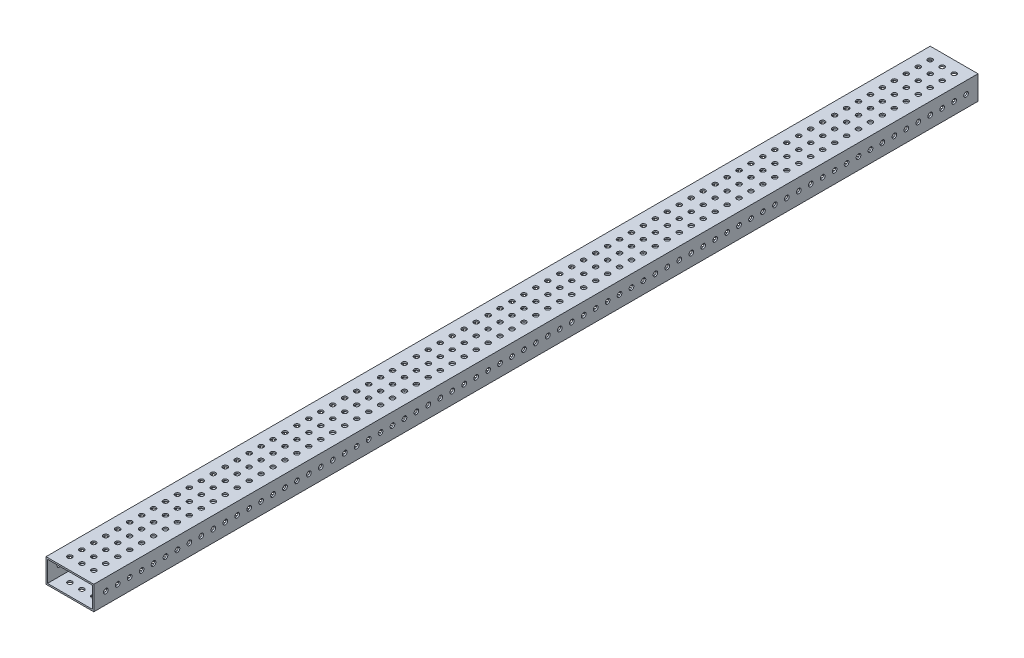
SolidWorks part; units mm, degrees
material "6061 Alloy"
ref_plane "Front Plane" through (0, 0, 0) normal (0, 0, 1) x (1, 0, 0)
ref_plane "Top Plane" through (0, 0, 0) normal (0, 1, 0) x (1, 0, 0)
ref_plane "Right Plane" through (0, 0, 0) normal (1, 0, 0) x (0, 0, -1)
sketch "Sketch1" plane through (0, 0, 0) normal (0, 0, 1) x (1, 0, 0)
  line L0 (1.5875, 1.5875) -> (49.2125, 1.5875)
  line L1 (0, 0) -> (50.8, 0)
  line L2 (0, 0) -> (0, 25.4)
  line L3 (0, 25.4) -> (50.8, 25.4)
  line L4 (50.8, 0) -> (50.8, 25.4)
  line L5 (49.2125, 1.5875) -> (49.2125, 23.8125)
  line L6 (1.5875, 23.8125) -> (49.2125, 23.8125)
  line L7 (1.5875, 1.5875) -> (1.5875, 23.8125)
  dimension "D1" = 50.8
  dimension "D2" = 25.4
  dimension "D3" = 1.5875
extrude "Boss-Extrude1" add sketch "Sketch1" along normal blind 939.8
sketch "Sketch2" plane through (50.8, 0, 0) normal (1, 0, 0) x (0, 0, -1)
  line L0 (-939.8, 0) -> (-939.8, 25.4) construction
  line L1 (-927.1, 12.7) -> (-914.4, 12.7) construction
  circle A0 centre (-927.1, 12.7) radius 2.4892
  circle A1 centre (-914.4, 12.7) radius 2.4892
  circle A2 centre (-901.7, 12.7) radius 2.4892
  circle A3 centre (-889, 12.7) radius 2.4892
  circle A4 centre (-876.3, 12.7) radius 2.4892
  circle A5 centre (-863.6, 12.7) radius 2.4892
  circle A6 centre (-850.9, 12.7) radius 2.4892
  circle A7 centre (-838.2, 12.7) radius 2.4892
  circle A8 centre (-825.5, 12.7) radius 2.4892
  circle A9 centre (-812.8, 12.7) radius 2.4892
  circle A10 centre (-800.1, 12.7) radius 2.4892
  circle A11 centre (-787.4, 12.7) radius 2.4892
  circle A12 centre (-774.7, 12.7) radius 2.4892
  circle A13 centre (-762, 12.7) radius 2.4892
  circle A14 centre (-749.3, 12.7) radius 2.4892
  circle A15 centre (-736.6, 12.7) radius 2.4892
  circle A16 centre (-723.9, 12.7) radius 2.4892
  circle A17 centre (-711.2, 12.7) radius 2.4892
  circle A18 centre (-698.5, 12.7) radius 2.4892
  circle A19 centre (-685.8, 12.7) radius 2.4892
  circle A20 centre (-673.1, 12.7) radius 2.4892
  circle A21 centre (-660.4, 12.7) radius 2.4892
  circle A22 centre (-647.7, 12.7) radius 2.4892
  circle A23 centre (-635, 12.7) radius 2.4892
  circle A24 centre (-622.3, 12.7) radius 2.4892
  circle A25 centre (-609.6, 12.7) radius 2.4892
  circle A26 centre (-596.9, 12.7) radius 2.4892
  circle A27 centre (-584.2, 12.7) radius 2.4892
  circle A28 centre (-571.5, 12.7) radius 2.4892
  circle A29 centre (-558.8, 12.7) radius 2.4892
  circle A30 centre (-546.1, 12.7) radius 2.4892
  circle A31 centre (-533.4, 12.7) radius 2.4892
  circle A32 centre (-520.7, 12.7) radius 2.4892
  circle A33 centre (-508, 12.7) radius 2.4892
  circle A34 centre (-495.3, 12.7) radius 2.4892
  circle A35 centre (-482.6, 12.7) radius 2.4892
  circle A36 centre (-469.9, 12.7) radius 2.4892
  circle A37 centre (-457.2, 12.7) radius 2.4892
  circle A38 centre (-444.5, 12.7) radius 2.4892
  circle A39 centre (-431.8, 12.7) radius 2.4892
  circle A40 centre (-419.1, 12.7) radius 2.4892
  circle A41 centre (-406.4, 12.7) radius 2.4892
  circle A42 centre (-393.7, 12.7) radius 2.4892
  circle A43 centre (-381, 12.7) radius 2.4892
  circle A44 centre (-368.3, 12.7) radius 2.4892
  circle A45 centre (-355.6, 12.7) radius 2.4892
  circle A46 centre (-342.9, 12.7) radius 2.4892
  circle A47 centre (-330.2, 12.7) radius 2.4892
  circle A48 centre (-317.5, 12.7) radius 2.4892
  circle A49 centre (-304.8, 12.7) radius 2.4892
  circle A50 centre (-292.1, 12.7) radius 2.4892
  circle A51 centre (-279.4, 12.7) radius 2.4892
  circle A52 centre (-266.7, 12.7) radius 2.4892
  circle A53 centre (-254, 12.7) radius 2.4892
  circle A54 centre (-241.3, 12.7) radius 2.4892
  circle A55 centre (-228.6, 12.7) radius 2.4892
  circle A56 centre (-215.9, 12.7) radius 2.4892
  circle A57 centre (-203.2, 12.7) radius 2.4892
  circle A58 centre (-190.5, 12.7) radius 2.4892
  circle A59 centre (-177.8, 12.7) radius 2.4892
  circle A60 centre (-165.1, 12.7) radius 2.4892
  circle A61 centre (-152.4, 12.7) radius 2.4892
  circle A62 centre (-139.7, 12.7) radius 2.4892
  circle A63 centre (-127, 12.7) radius 2.4892
  circle A64 centre (-114.3, 12.7) radius 2.4892
  circle A65 centre (-101.6, 12.7) radius 2.4892
  circle A66 centre (-88.9, 12.7) radius 2.4892
  circle A67 centre (-76.2, 12.7) radius 2.4892
  circle A68 centre (-63.5, 12.7) radius 2.4892
  circle A69 centre (-50.8, 12.7) radius 2.4892
  circle A70 centre (-38.1, 12.7) radius 2.4892
  circle A71 centre (-25.4, 12.7) radius 2.4892
  circle A72 centre (-12.7, 12.7) radius 2.4892
  point P4 (-939.8, 12.7)
  dimension "D1" = 4.9784
  dimension "D2" = 12.7
  dimension "D4" = 12.7
  dimension "D3" = 73
extrude "Cut-Extrude1" cut sketch "Sketch2" against normal through all
sketch "Sketch3" plane through (0, 25.4, 0) normal (0, 1, 0) x (1, 0, 0)
  line L0 (0, -939.8) -> (0, 0) construction
  line L1 (50.8, 0) -> (0, 0) construction
  line L2 (12.7, -12.7) -> (25.4, -12.7) construction
  line L3 (12.7, -12.7) -> (12.7, -25.4) construction
  circle A0 centre (12.7, -12.7) radius 2.4892
  circle A1 centre (25.4, -12.7) radius 2.4892
  circle A2 centre (38.1, -12.7) radius 2.4892
  circle A3 centre (25.4, -25.4) radius 2.4892
  circle A4 centre (38.1, -25.4) radius 2.4892
  circle A5 centre (25.4, -38.1) radius 2.4892
  circle A6 centre (38.1, -38.1) radius 2.4892
  circle A7 centre (25.4, -50.8) radius 2.4892
  circle A8 centre (38.1, -50.8) radius 2.4892
  circle A9 centre (25.4, -63.5) radius 2.4892
  circle A10 centre (38.1, -63.5) radius 2.4892
  circle A11 centre (25.4, -76.2) radius 2.4892
  circle A12 centre (38.1, -76.2) radius 2.4892
  circle A13 centre (25.4, -88.9) radius 2.4892
  circle A14 centre (38.1, -88.9) radius 2.4892
  circle A15 centre (25.4, -101.6) radius 2.4892
  circle A16 centre (38.1, -101.6) radius 2.4892
  circle A17 centre (25.4, -114.3) radius 2.4892
  circle A18 centre (38.1, -114.3) radius 2.4892
  circle A19 centre (25.4, -127) radius 2.4892
  circle A20 centre (38.1, -127) radius 2.4892
  circle A21 centre (25.4, -139.7) radius 2.4892
  circle A22 centre (38.1, -139.7) radius 2.4892
  circle A23 centre (25.4, -152.4) radius 2.4892
  circle A24 centre (38.1, -152.4) radius 2.4892
  circle A25 centre (25.4, -165.1) radius 2.4892
  circle A26 centre (38.1, -165.1) radius 2.4892
  circle A27 centre (25.4, -177.8) radius 2.4892
  circle A28 centre (38.1, -177.8) radius 2.4892
  circle A29 centre (25.4, -190.5) radius 2.4892
  circle A30 centre (38.1, -190.5) radius 2.4892
  circle A31 centre (25.4, -203.2) radius 2.4892
  circle A32 centre (38.1, -203.2) radius 2.4892
  circle A33 centre (25.4, -215.9) radius 2.4892
  circle A34 centre (38.1, -215.9) radius 2.4892
  circle A35 centre (25.4, -228.6) radius 2.4892
  circle A36 centre (38.1, -228.6) radius 2.4892
  circle A37 centre (25.4, -241.3) radius 2.4892
  circle A38 centre (38.1, -241.3) radius 2.4892
  circle A39 centre (25.4, -254) radius 2.4892
  circle A40 centre (38.1, -254) radius 2.4892
  circle A41 centre (25.4, -266.7) radius 2.4892
  circle A42 centre (38.1, -266.7) radius 2.4892
  circle A43 centre (25.4, -279.4) radius 2.4892
  circle A44 centre (38.1, -279.4) radius 2.4892
  circle A45 centre (25.4, -292.1) radius 2.4892
  circle A46 centre (38.1, -292.1) radius 2.4892
  circle A47 centre (25.4, -304.8) radius 2.4892
  circle A48 centre (38.1, -304.8) radius 2.4892
  circle A49 centre (25.4, -317.5) radius 2.4892
  circle A50 centre (38.1, -317.5) radius 2.4892
  circle A51 centre (25.4, -330.2) radius 2.4892
  circle A52 centre (38.1, -330.2) radius 2.4892
  circle A53 centre (25.4, -342.9) radius 2.4892
  circle A54 centre (38.1, -342.9) radius 2.4892
  circle A55 centre (25.4, -355.6) radius 2.4892
  circle A56 centre (38.1, -355.6) radius 2.4892
  circle A57 centre (25.4, -368.3) radius 2.4892
  circle A58 centre (38.1, -368.3) radius 2.4892
  circle A59 centre (25.4, -381) radius 2.4892
  circle A60 centre (38.1, -381) radius 2.4892
  circle A61 centre (25.4, -393.7) radius 2.4892
  circle A62 centre (38.1, -393.7) radius 2.4892
  circle A63 centre (25.4, -406.4) radius 2.4892
  circle A64 centre (38.1, -406.4) radius 2.4892
  circle A65 centre (25.4, -419.1) radius 2.4892
  circle A66 centre (38.1, -419.1) radius 2.4892
  circle A67 centre (25.4, -431.8) radius 2.4892
  circle A68 centre (38.1, -431.8) radius 2.4892
  circle A69 centre (25.4, -444.5) radius 2.4892
  circle A70 centre (38.1, -444.5) radius 2.4892
  circle A71 centre (25.4, -457.2) radius 2.4892
  circle A72 centre (38.1, -457.2) radius 2.4892
  circle A73 centre (25.4, -469.9) radius 2.4892
  circle A74 centre (38.1, -469.9) radius 2.4892
  circle A75 centre (25.4, -482.6) radius 2.4892
  circle A76 centre (38.1, -482.6) radius 2.4892
  circle A77 centre (25.4, -495.3) radius 2.4892
  circle A78 centre (38.1, -495.3) radius 2.4892
  circle A79 centre (25.4, -508) radius 2.4892
  circle A80 centre (38.1, -508) radius 2.4892
  circle A81 centre (25.4, -520.7) radius 2.4892
  circle A82 centre (38.1, -520.7) radius 2.4892
  circle A83 centre (25.4, -533.4) radius 2.4892
  circle A84 centre (38.1, -533.4) radius 2.4892
  circle A85 centre (25.4, -546.1) radius 2.4892
  circle A86 centre (38.1, -546.1) radius 2.4892
  circle A87 centre (25.4, -558.8) radius 2.4892
  circle A88 centre (38.1, -558.8) radius 2.4892
  circle A89 centre (25.4, -571.5) radius 2.4892
  circle A90 centre (38.1, -571.5) radius 2.4892
  circle A91 centre (25.4, -584.2) radius 2.4892
  circle A92 centre (38.1, -584.2) radius 2.4892
  circle A93 centre (25.4, -596.9) radius 2.4892
  circle A94 centre (38.1, -596.9) radius 2.4892
  circle A95 centre (25.4, -609.6) radius 2.4892
  circle A96 centre (38.1, -609.6) radius 2.4892
  circle A97 centre (25.4, -622.3) radius 2.4892
  circle A98 centre (38.1, -622.3) radius 2.4892
  circle A99 centre (25.4, -635) radius 2.4892
  circle A100 centre (38.1, -635) radius 2.4892
  circle A101 centre (25.4, -647.7) radius 2.4892
  circle A102 centre (38.1, -647.7) radius 2.4892
  circle A103 centre (25.4, -660.4) radius 2.4892
  circle A104 centre (38.1, -660.4) radius 2.4892
  circle A105 centre (25.4, -673.1) radius 2.4892
  circle A106 centre (38.1, -673.1) radius 2.4892
  circle A107 centre (25.4, -685.8) radius 2.4892
  circle A108 centre (38.1, -685.8) radius 2.4892
  circle A109 centre (25.4, -698.5) radius 2.4892
  circle A110 centre (38.1, -698.5) radius 2.4892
  circle A111 centre (25.4, -711.2) radius 2.4892
  circle A112 centre (38.1, -711.2) radius 2.4892
  circle A113 centre (25.4, -723.9) radius 2.4892
  circle A114 centre (38.1, -723.9) radius 2.4892
  circle A115 centre (25.4, -736.6) radius 2.4892
  circle A116 centre (38.1, -736.6) radius 2.4892
  circle A117 centre (25.4, -749.3) radius 2.4892
  circle A118 centre (38.1, -749.3) radius 2.4892
  circle A119 centre (25.4, -762) radius 2.4892
  circle A120 centre (38.1, -762) radius 2.4892
  circle A121 centre (25.4, -774.7) radius 2.4892
  circle A122 centre (38.1, -774.7) radius 2.4892
  circle A123 centre (25.4, -787.4) radius 2.4892
  circle A124 centre (38.1, -787.4) radius 2.4892
  circle A125 centre (25.4, -800.1) radius 2.4892
  circle A126 centre (38.1, -800.1) radius 2.4892
  circle A127 centre (25.4, -812.8) radius 2.4892
  circle A128 centre (38.1, -812.8) radius 2.4892
  circle A129 centre (25.4, -825.5) radius 2.4892
  circle A130 centre (38.1, -825.5) radius 2.4892
  circle A131 centre (25.4, -838.2) radius 2.4892
  circle A132 centre (38.1, -838.2) radius 2.4892
  circle A133 centre (25.4, -850.9) radius 2.4892
  circle A134 centre (38.1, -850.9) radius 2.4892
  circle A135 centre (25.4, -863.6) radius 2.4892
  circle A136 centre (38.1, -863.6) radius 2.4892
  circle A137 centre (25.4, -876.3) radius 2.4892
  circle A138 centre (38.1, -876.3) radius 2.4892
  circle A139 centre (25.4, -889) radius 2.4892
  circle A140 centre (38.1, -889) radius 2.4892
  circle A141 centre (25.4, -901.7) radius 2.4892
  circle A142 centre (38.1, -901.7) radius 2.4892
  circle A143 centre (25.4, -914.4) radius 2.4892
  circle A144 centre (38.1, -914.4) radius 2.4892
  circle A145 centre (25.4, -927.1) radius 2.4892
  circle A146 centre (38.1, -927.1) radius 2.4892
  circle A149 centre (12.7, -25.4) radius 2.4892
  circle A150 centre (12.7, -38.1) radius 2.4892
  circle A151 centre (12.7, -50.8) radius 2.4892
  circle A152 centre (12.7, -63.5) radius 2.4892
  circle A153 centre (12.7, -76.2) radius 2.4892
  circle A154 centre (12.7, -88.9) radius 2.4892
  circle A155 centre (12.7, -101.6) radius 2.4892
  circle A156 centre (12.7, -114.3) radius 2.4892
  circle A157 centre (12.7, -127) radius 2.4892
  circle A158 centre (12.7, -139.7) radius 2.4892
  circle A159 centre (12.7, -152.4) radius 2.4892
  circle A160 centre (12.7, -165.1) radius 2.4892
  circle A161 centre (12.7, -177.8) radius 2.4892
  circle A162 centre (12.7, -190.5) radius 2.4892
  circle A163 centre (12.7, -203.2) radius 2.4892
  circle A164 centre (12.7, -215.9) radius 2.4892
  circle A165 centre (12.7, -228.6) radius 2.4892
  circle A166 centre (12.7, -241.3) radius 2.4892
  circle A167 centre (12.7, -254) radius 2.4892
  circle A168 centre (12.7, -266.7) radius 2.4892
  circle A169 centre (12.7, -279.4) radius 2.4892
  circle A170 centre (12.7, -292.1) radius 2.4892
  circle A171 centre (12.7, -304.8) radius 2.4892
  circle A172 centre (12.7, -317.5) radius 2.4892
  circle A173 centre (12.7, -330.2) radius 2.4892
  circle A174 centre (12.7, -342.9) radius 2.4892
  circle A175 centre (12.7, -355.6) radius 2.4892
  circle A176 centre (12.7, -368.3) radius 2.4892
  circle A177 centre (12.7, -381) radius 2.4892
  circle A178 centre (12.7, -393.7) radius 2.4892
  circle A179 centre (12.7, -406.4) radius 2.4892
  circle A180 centre (12.7, -419.1) radius 2.4892
  circle A181 centre (12.7, -431.8) radius 2.4892
  circle A182 centre (12.7, -444.5) radius 2.4892
  circle A183 centre (12.7, -457.2) radius 2.4892
  circle A184 centre (12.7, -469.9) radius 2.4892
  circle A185 centre (12.7, -482.6) radius 2.4892
  circle A186 centre (12.7, -495.3) radius 2.4892
  circle A187 centre (12.7, -508) radius 2.4892
  circle A188 centre (12.7, -520.7) radius 2.4892
  circle A189 centre (12.7, -533.4) radius 2.4892
  circle A190 centre (12.7, -546.1) radius 2.4892
  circle A191 centre (12.7, -558.8) radius 2.4892
  circle A192 centre (12.7, -571.5) radius 2.4892
  circle A193 centre (12.7, -584.2) radius 2.4892
  circle A194 centre (12.7, -596.9) radius 2.4892
  circle A195 centre (12.7, -609.6) radius 2.4892
  circle A196 centre (12.7, -622.3) radius 2.4892
  circle A197 centre (12.7, -635) radius 2.4892
  circle A198 centre (12.7, -647.7) radius 2.4892
  circle A199 centre (12.7, -660.4) radius 2.4892
  circle A200 centre (12.7, -673.1) radius 2.4892
  circle A201 centre (12.7, -685.8) radius 2.4892
  circle A202 centre (12.7, -698.5) radius 2.4892
  circle A203 centre (12.7, -711.2) radius 2.4892
  circle A204 centre (12.7, -723.9) radius 2.4892
  circle A205 centre (12.7, -736.6) radius 2.4892
  circle A206 centre (12.7, -749.3) radius 2.4892
  circle A207 centre (12.7, -762) radius 2.4892
  circle A208 centre (12.7, -774.7) radius 2.4892
  circle A209 centre (12.7, -787.4) radius 2.4892
  circle A210 centre (12.7, -800.1) radius 2.4892
  circle A211 centre (12.7, -812.8) radius 2.4892
  circle A212 centre (12.7, -825.5) radius 2.4892
  circle A213 centre (12.7, -838.2) radius 2.4892
  circle A214 centre (12.7, -850.9) radius 2.4892
  circle A215 centre (12.7, -863.6) radius 2.4892
  circle A216 centre (12.7, -876.3) radius 2.4892
  circle A217 centre (12.7, -889) radius 2.4892
  circle A218 centre (12.7, -901.7) radius 2.4892
  circle A219 centre (12.7, -914.4) radius 2.4892
  circle A220 centre (12.7, -927.1) radius 2.4892
  dimension "D1" = 4.9784
  dimension "D2" = 12.7
  dimension "D3" = 12.7
  dimension "D6" = 90
  dimension "D7" = 12.7
  dimension "D8" = 12.7
  dimension "D4" = 3
  dimension "D5" = 73
extrude "Cut-Extrude2" cut sketch "Sketch3" against normal through all
